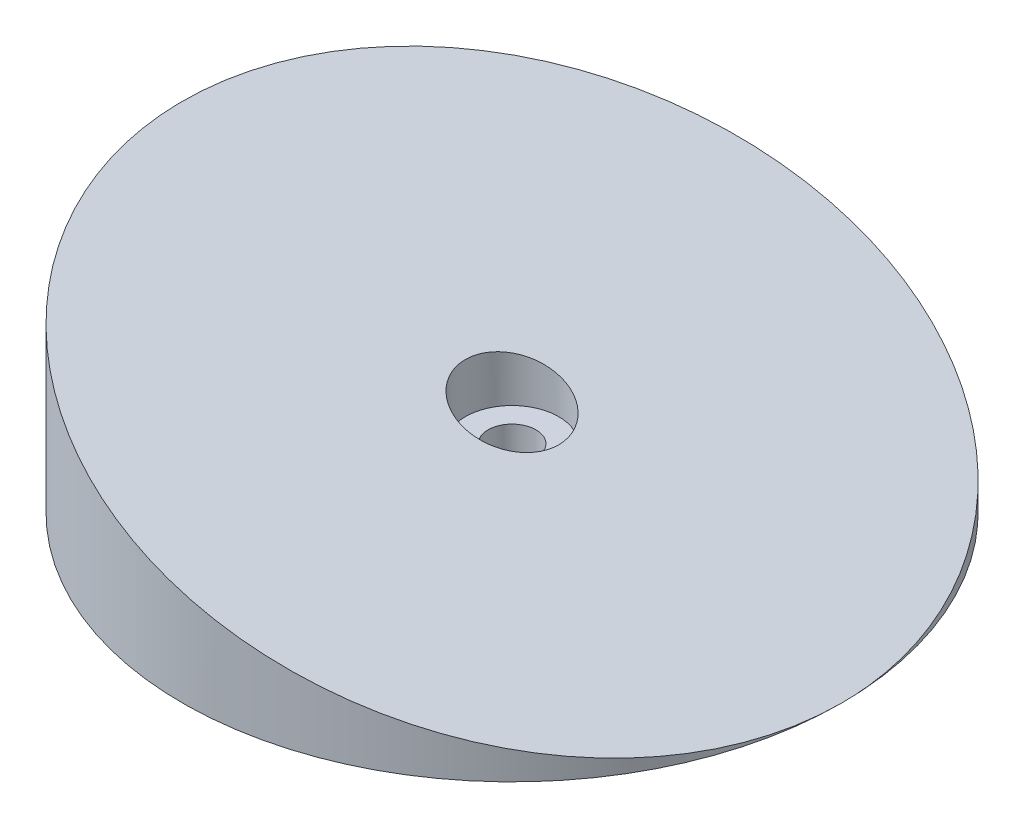
SolidWorks part; units mm, degrees
ref_plane "Front Plane" through (0, 0, 0) normal (0, 0, 1) x (1, 0, 0)
ref_plane "Top Plane" through (0, 0, 0) normal (0, 1, 0) x (1, 0, 0)
ref_plane "Right Plane" through (0, 0, 0) normal (1, 0, 0) x (0, 0, -1)
sketch "Sketch1" plane through (0, 0, 0) normal (0, 1, 0) x (1, 0, 0)
  circle A0 centre (0, 0) radius 55
  circle A1 centre (0, 0) radius 4
  dimension "D1" = 110
  dimension "D2" = 8
extrude "Boss-Extrude1" add sketch "Sketch1" along normal blind 32
sketch "Sketch2" plane through (0, 0, 0) normal (0, 0, 1) x (1, 0, 0)
  line L0 (55, 0) -> (-55, 0) construction
  line L1 (-55, 0) -> (-55, 32) construction
  line L2 (-55, 32) -> (55, 32) construction
  line L3 (0, 32) -> (0, 0) construction
  line L4 (55, 0) -> (55, 32) construction
  dimension "D1" = 55
  dimension "D2" = 32
sketch "Sketch3" plane through (0, 0, 0) normal (0, 0, 1) x (1, 0, 0)
  line L0 (55, 0) -> (55, 32) construction
  line L1 (55, 0) -> (-55, 0) construction
  line L2 (-55, 0) -> (-55, 32) construction
  line L3 (-55, 32) -> (55, 32) construction
  line L4 (55, 0) -> (55, 32)
  line L5 (55, 0) -> (-55, 0) construction
  line L6 (-55, 0) -> (-55, 32) construction
  line L7 (-55, 32) -> (55, 32)
  line L8 (-55, 32) -> (55, 0)
extrude "Cut-Extrude1" cut sketch "Sketch3" against normal through all and the other way through all
ref_plane "Plane1" through (0, 10, 0) normal (0, 1, 0) x (1, 0, 0)
sketch "Sketch4" plane through (0, 10, 0) normal (0, 1, 0) x (1, 0, 0)
  circle A0 centre (0, 0) radius 7.7966
extrude "Cut-Extrude2" cut sketch "Sketch4" along normal through all
